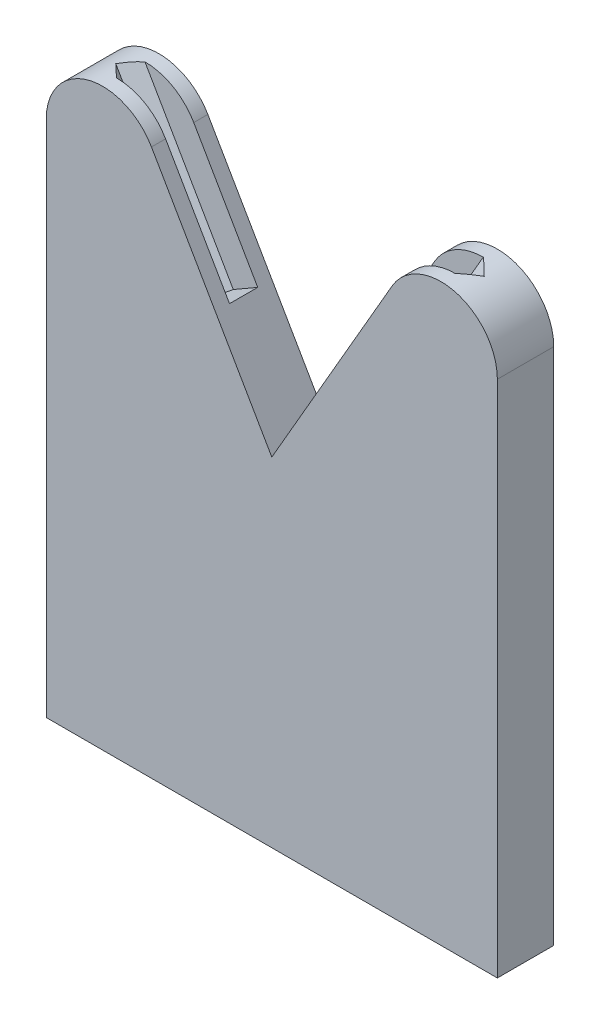
SolidWorks part; units mm, degrees
material "6061 Alloy"
ref_plane "Front" through (0, 0, 0) normal (0, 0, 1) x (1, 0, 0)
ref_plane "Top" through (0, 0, 0) normal (0, 1, 0) x (1, 0, 0)
ref_plane "Right" through (0, 0, 0) normal (1, 0, 0) x (0, 0, -1)
sketch "Sketch1" plane through (0, 0, 0) normal (0, 0, 1) x (1, 0, 0)
  line L0 (-50.8, 87.9882) -> (0, 0)
  line L5 (0, 0) -> (50.8, 87.9882)
  line L6 (50.8, 87.9882) -> (50.8, -76.2)
  line L7 (50.8, -76.2) -> (-50.8, -76.2)
  line L8 (-50.8, -76.2) -> (-50.8, 87.9882)
  point P6 (0, 0)
  point P7 (41.8436, 73.422)
  dimension "D1" = 30
  dimension "D2" = 101.6
  dimension "D3" = 76.2
extrude "Boss-Extrude1" add sketch "Sketch1" along normal mid plane 12.7
ref_plane "Plane1" through (-50.8, 87.9882, 0) normal (-0.5, 0.866, 0) x (0, 0, -1)
sketch "Sketch2" plane through (-50.8, 87.9882, 0) normal (-0.5, 0.866, 0) x (0, 0, -1)
  line L4 (3.175, 0) -> (-3.175, 0)
  line L5 (-3.175, 0) -> (-3.175, 6.35)
  line L6 (-3.175, 6.35) -> (0, 9.525)
  line L7 (0, 9.525) -> (3.175, 6.35)
  line L8 (3.175, 6.35) -> (3.175, 0)
  line L9 (-6.35, 0) -> (6.35, 0) construction
  point P9 (0, 0)
  point P10 (0, 0)
  point P11 (0, 0)
  point P14 (0, 0)
  dimension "D1" = 6.35
  dimension "D2" = 6.35
extrude "Cut-Extrude1" cut sketch "Sketch2" against normal blind 76.2
mirror "Mirror5" about plane through (0, 0, 0) normal (1, 0, 0) of "Cut-Extrude1"
fillet "Fillet1" radius 12.7 2 edges at (50.8, 87.9882, 4.7625) (-50.8, 87.9882, -4.7625)
